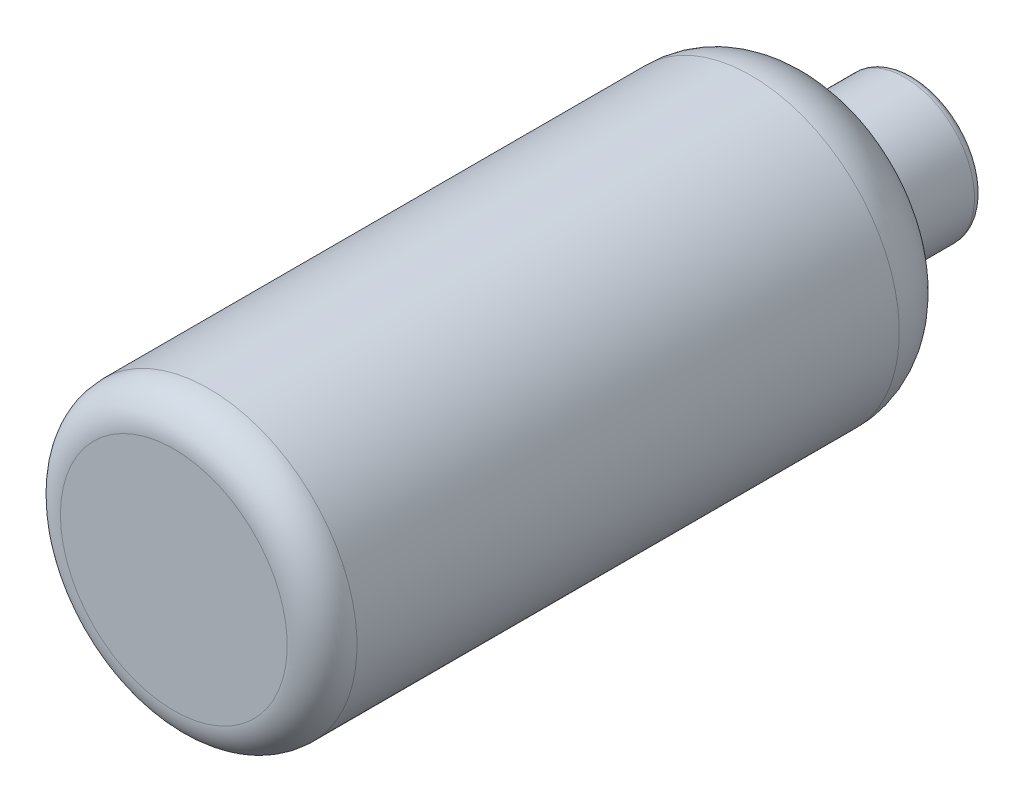
SolidWorks part; units mm, degrees
material "6061-T6 (SS)"
ref_plane "Front Plane" through (0, 0, 0) normal (0, 0, 1) x (1, 0, 0)
ref_plane "Top Plane" through (0, 0, 0) normal (0, 1, 0) x (1, 0, 0)
ref_plane "Right Plane" through (0, 0, 0) normal (1, 0, 0) x (0, 0, -1)
sketch "Sketch2" plane through (0, 0, 0) normal (0, 1, 0) x (1, 0, 0)
  line L0 (0, 0) -> (20.6375, 0)
  line L1 (26.9875, 6.35) -> (26.9875, 105.0503)
  line L3 (12.7, 120.8458) -> (12.7, 133.0325)
  line L6 (0, 2.54) -> (20.6375, 2.54)
  line L7 (24.4475, 6.35) -> (24.4475, 105.0503)
  line L8 (10.16, 120.8458) -> (10.16, 134.62)
  line L9 (10.16, 134.62) -> (11.1125, 134.62)
  line L11 (2.54, 132.08) -> (10.16, 132.08) construction
  line L12 (2.54, 2.54) -> (20.6375, 2.54) construction
  line L13 (2.54, 2.54) -> (2.54, 132.08) construction
  line L14 (0, 0) -> (0, 134.62) construction
  line L15 (0, 0) -> (0, 2.54)
  line L16 (24.4475, 6.35) -> (26.9875, 6.35)
  line L17 (24.4475, 105.0503) -> (26.9875, 105.0503)
  line L18 (10.16, 120.8458) -> (12.7, 120.8458)
  line L19 (0, 132.08) -> (0, 2.54) construction
  line L20 (10.16, 120.8458) -> (10.16, 132.08) construction
  line L21 (0, 134.62) -> (11.1125, 134.62) construction
  arc A0 (26.9875, 6.35) -> (20.6375, 0) centre (20.6375, 6.35) cw
  arc A1 (26.9875, 105.0503) -> (15.5575, 117.6867) centre (14.2875, 105.0503) ccw
  arc A2 (12.7, 133.0325) -> (11.1125, 134.62) centre (11.1125, 133.0325) ccw
  arc A3 (12.7, 120.8458) -> (15.5575, 117.6867) centre (15.875, 120.8458) ccw
  arc A4 (24.4475, 6.35) -> (20.6375, 2.54) centre (20.6375, 6.35) cw
  arc A5 (24.4475, 105.0503) -> (15.3035, 115.1594) centre (14.2875, 105.0503) ccw
  arc A6 (10.16, 120.8458) -> (15.3035, 115.1594) centre (15.875, 120.8458) ccw
  arc A7 (10.16, 132.08) -> (10.16, 132.08) centre (10.16, 132.08) ccw
  point P9 (26.9875, 0)
  point P14 (12.7, 134.62)
  dimension "D5" = 6.35
  dimension "D6" = 12.7
  dimension "D7" = 1.5875
  dimension "D3" = 3.175
  dimension "D1" = 26.9875
  dimension "D2" = 12.7
  dimension "D4" = 134.62
  dimension "D9" = 2.54
revolve "Revolve2" add sketch "Sketch2" angle 360 about L19
